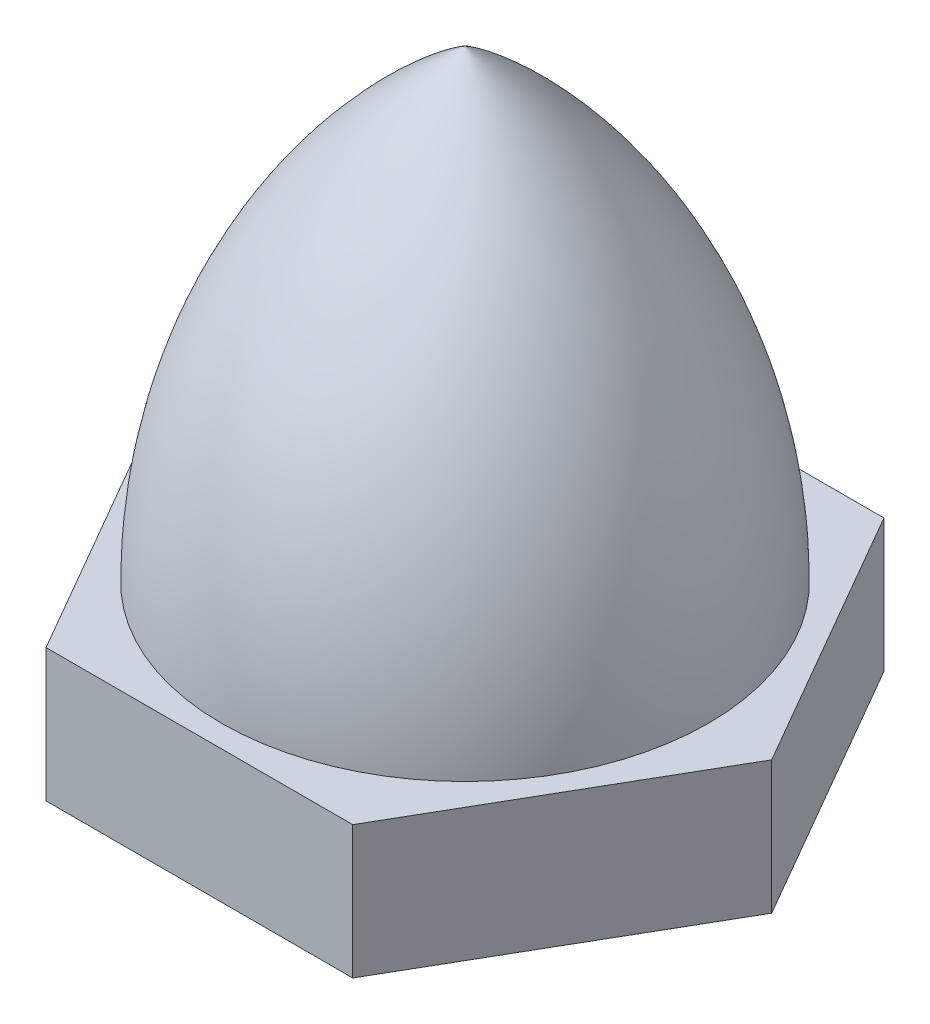
SolidWorks part; units mm, degrees
material "6061 Alloy"
ref_plane "Front" through (0, 0, 0) normal (0, 0, 1) x (1, 0, 0)
ref_plane "Top" through (0, 0, 0) normal (0, 1, 0) x (1, 0, 0)
ref_plane "Right" through (0, 0, 0) normal (1, 0, 0) x (0, 0, -1)
sketch "Sketch1" plane through (0, 0, 0) normal (0, 1, 0) x (1, 0, 0)
  line L1 (6.9282, 0) -> (3.4641, 6)
  line L2 (3.4641, 6) -> (-3.4641, 6)
  line L3 (-3.4641, 6) -> (-6.9282, 0)
  line L4 (-6.9282, 0) -> (-3.4641, -6)
  line L5 (-3.4641, -6) -> (3.4641, -6)
  line L6 (3.4641, -6) -> (6.9282, 0)
  circle A0 centre (0, 0) radius 6 construction
  dimension "D1" = 12
extrude "Boss-Extrude1" add sketch "Sketch1" along normal blind 3
sketch "Sketch2" plane through (0, 0, 0) normal (0, 0, 1) x (1, 0, 0)
  line L0 (0, 3) -> (0, 13.5)
  line L1 (-3.4641, 3) -> (3.4641, 3) construction
  line L2 (3.4641, 3) -> (6.9282, 3) construction
  line L3 (5.5, 3) -> (5.5, -3.7743) construction
  line L4 (0, 0) -> (0, -4.3073) construction
  line L5 (0, 3) -> (5.5, 3)
  arc A0 (0, 13.5) -> (5.5, 3) centre (-7.2727, 3) cw
  dimension "D1" = 11
  dimension "D2" = 10.5
revolve "Revolve1" add sketch "Sketch2" angle 360 about L0
hole_wizard "M6 Tapped Hole1" positions "Sketch4" profile "Sketch3" tap size "M6" standard "ISO"
sketch "Sketch4" plane through (0, 0, 0) normal (0, -1, 0) x (-1, 0, 0)
  point P0 (0, 0)
sketch "Sketch3" plane through (0, 0, 0) normal (1, 0, 0) x (0, 0, -1)
  line L0 (0, 0) -> (0, 11.5022)
  line L1 (0, 11.5022) -> (2.5, 10)
  line L2 (2.5, 10) -> (2.5, 0)
  line L5 (2.5, 0) -> (0, 0)
  line L10 (0, 11.5022) -> (-2.5, 10) construction
  line L11 (0, -6.35) -> (0, 107.95) construction
  dimension "Tap Drill Dia." = 5
  dimension "Tap Drill Depth" = 10
  dimension "Drill Angle" = 118
cosmetic thread "Hole Thread1" parameters "D1"=10, "D2"=6
